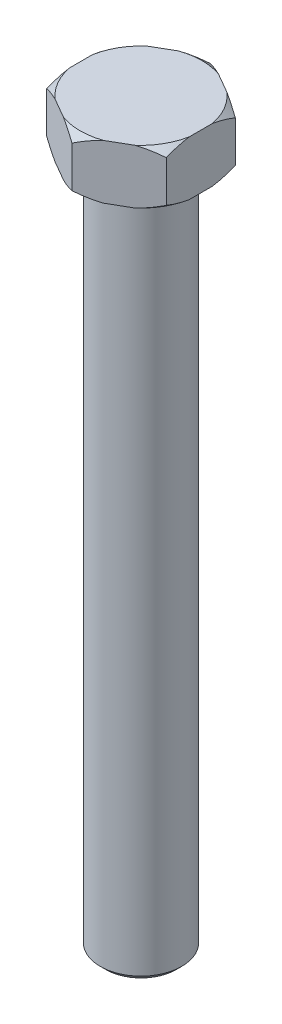
SolidWorks part; units mm, degrees
ref_plane "Front" through (0, 0, 0) normal (0, 0, 1) x (1, 0, 0)
ref_plane "Top" through (0, 0, 0) normal (0, 1, 0) x (1, 0, 0)
ref_plane "Right" through (0, 0, 0) normal (1, 0, 0) x (0, 0, -1)
sketch "Sketch1" plane through (0, 0, 0) normal (0, 1, 0) x (1, 0, 0)
  line L1 (0, 12.7017) -> (-11, 6.3509)
  line L2 (-11, 6.3509) -> (-11, -6.3509)
  line L3 (-11, -6.3509) -> (0, -12.7017)
  line L4 (0, -12.7017) -> (11, -6.3509)
  line L5 (11, -6.3509) -> (11, 6.3509)
  line L6 (11, 6.3509) -> (0, 12.7017)
  circle A0 centre (0, 0) radius 11 construction
  point P1 (0, 0)
  dimension "D1" = 22
extrude "Boss-Extrude1" add sketch "Sketch1" along normal blind 10
sketch "Sketch2" plane through (0, 0, 0) normal (0, -1, 0) x (1, 0, 0)
  circle A0 centre (0, 0) radius 7.5
  dimension "D1" = 15
extrude "Boss-Extrude2" add sketch "Sketch2" along normal blind 126
cosmetic thread "Cosmetic Thread1" parameters "D1"=19, "D2"=6.619
sketch "Sketch4" plane through (0, 0, 0) normal (1, 0, 0) x (0, 0, -1)
  line L0 (0, 0) -> (0, 12.7667) construction
  line L1 (-7.5, 0) -> (7.5, 0) construction
  line L2 (-12.7017, 5) -> (12.7017, 5) construction
  line L3 (-12.7017, 10) -> (-12.7017, 0) construction
  line L4 (12.7017, 10) -> (12.7017, 0) construction
  line L5 (-12.7017, 10) -> (-12.7017, 8.8)
  line L6 (-12.7017, 0) -> (-12.7017, 1.2)
  line L7 (-12.7017, 8.8) -> (-11.2017, 10)
  line L9 (-12.7017, 1.2) -> (-11.2017, 0)
  line L10 (-11.2017, 10) -> (-12.7017, 10)
  line L11 (-11.2017, 0) -> (-12.7017, 0)
  dimension "D1" = 1.5
  dimension "D2" = 1.2
revolve "Cut-Revolve2" cut sketch "Sketch4" angle 360 about L0
chamfer "Chamfer1" distance 1 angle 45 1 edges at (0, -126, -7.5)
